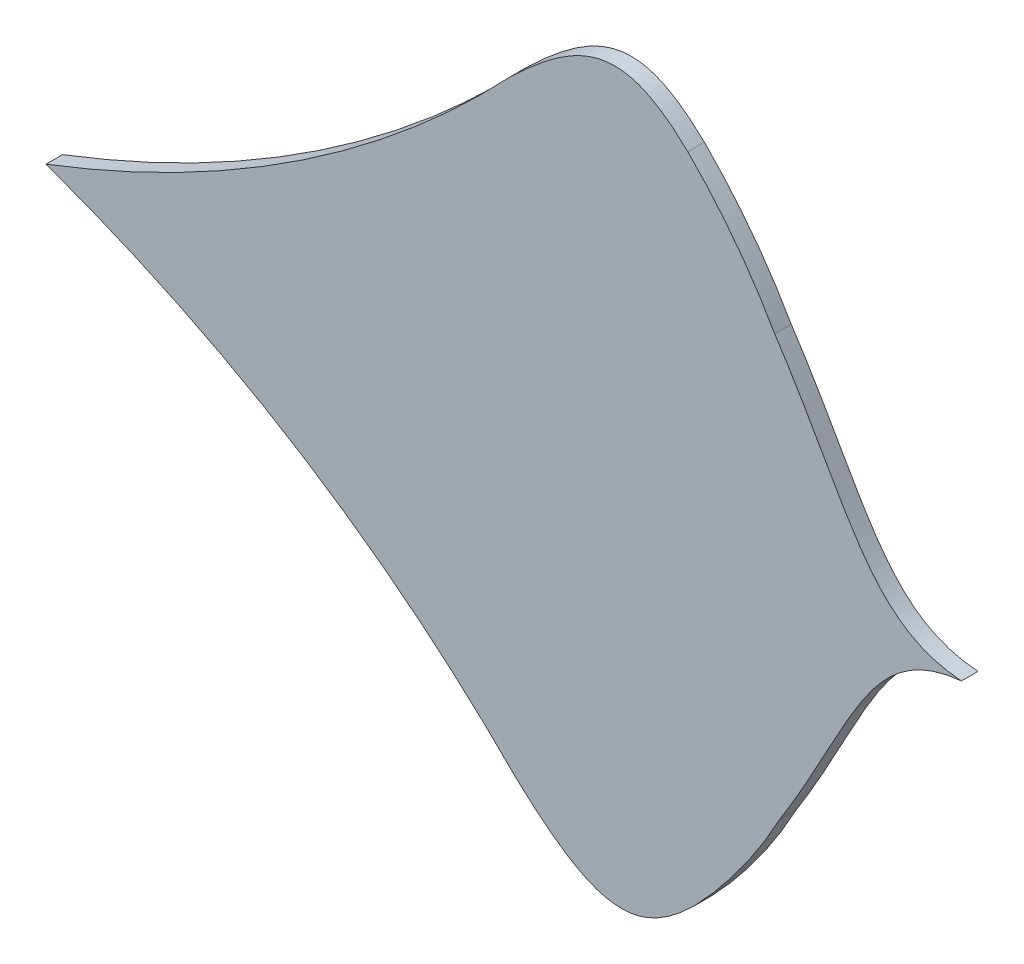
SolidWorks part; units mm, degrees
ref_plane "Front Plane" through (0, 0, 0) normal (0, 0, 1) x (1, 0, 0)
ref_plane "Top Plane" through (0, 0, 0) normal (0, 1, 0) x (1, 0, 0)
ref_plane "Right Plane" through (0, 0, 0) normal (1, 0, 0) x (0, 0, -1)
sketch "Sketch1" plane through (0, 0, 0) normal (0, 0, 1) x (1, 0, 0)
  line L0 (-934.3043, 428.0306) -> (340.3624, 428.0306) construction
  line L1 (532.9146, 433.1833) -> (-1140.3036, 414.6378) construction
  spline S0 degree 3 poles (409.2249, 431.8124) (353.2083, 435.815) (341.8018, 488.1617) (296.4468, 556.9762) knots 0 0 0 0 1 1 1 1
  spline S1 degree 3 poles (296.4468, 556.9762) (281.9328, 582.5892) (264.4059, 605.5916) (243.9607, 626.0369) knots 0 0 0 0 1 1 1 1
  spline S2 degree 3 poles (243.9607, 626.0369) (206.5685, 661.954) (181.0635, 654.3844) (136.2161, 611.032) knots 0 0 0 0 1 1 1 1
  spline S3 degree 2 poles (136.2161, 611.032) (21.1489, 488.8716) (-143.6069, 425.6849) knots 0 0 0 1 1 1
  spline S4 degree 3 poles (409.2249, 431.8124) (353.3108, 426.5691) (343.0674, 373.9825) (299.2487, 304.1796) knots 0 0 0 0 1 1 1 1
  spline S5 degree 3 poles (299.2487, 304.1796) (285.306, 278.2511) (268.2933, 254.8659) (248.3062, 233.9725) knots 0 0 0 0 1 1 1 1
  spline S6 degree 3 poles (248.3062, 233.9725) (211.7194, 197.2355) (186.0528, 204.2378) (140.2555, 246.5856) knots 0 0 0 0 1 1 1 1
  spline S7 degree 2 poles (140.2555, 246.5856) (22.509, 366.1655) (-143.6069, 425.6849) knots 0 0 0 1 1 1
extrude "Boss-Extrude1" add sketch "Sketch1" along normal blind 10 contours S4 S5 S6 S7 S3 S2 S1 S0
